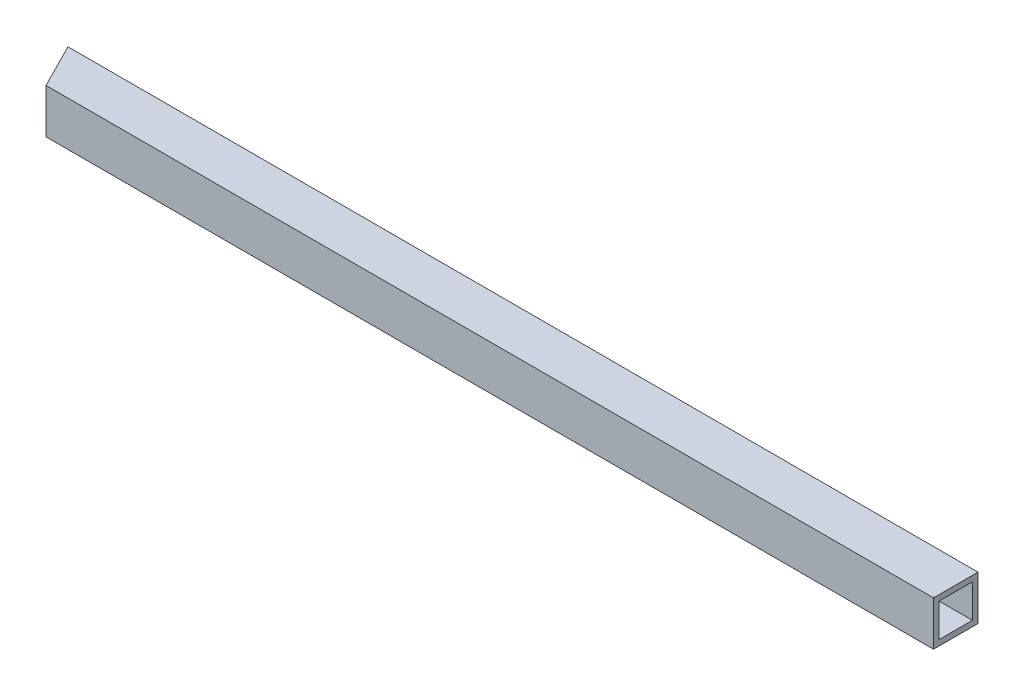
SolidWorks part; units mm, degrees
material "AISI 302"
ref_plane "Front Plane" through (0, 0, 0) normal (0, 0, 1) x (1, 0, 0)
ref_plane "Top Plane" through (0, 0, 0) normal (0, 1, 0) x (1, 0, 0)
ref_plane "Right Plane" through (0, 0, 0) normal (1, 0, 0) x (0, 0, -1)
sketch "Sketch2" plane through (0, 0, 0) normal (0, 0, 1) x (1, 0, 0)
  line L1 (0, 0) -> (4155.694, 0)
  line L2 (0, 0) -> (0, 203.2)
  line L3 (0, 203.2) -> (4155.694, 203.2)
  line L4 (4155.694, 0) -> (4155.694, 203.2)
  dimension "D1" = 203.2
  dimension "D2" = 4155.694
extrude "Boss-Extrude1" add sketch "Sketch2" along normal blind 203.2
sketch "Sketch3" plane through (0, 0, 0) normal (-1, 0, 0) x (0, 0, 1)
  line L8 (25.4, 25.4) -> (177.8, 25.4)
  line L9 (177.8, 25.4) -> (177.8, 177.8)
  line L10 (177.8, 177.8) -> (25.4, 177.8)
  line L11 (25.4, 177.8) -> (25.4, 25.4)
  line L12 (25.4, 25.4) -> (177.8, 25.4)
  line L13 (177.8, 25.4) -> (177.8, 177.8)
  line L14 (177.8, 177.8) -> (25.4, 177.8)
  line L15 (25.4, 177.8) -> (25.4, 25.4)
  dimension "D1" = 25.4
extrude "Cut-Extrude1" cut sketch "Sketch3" against normal through all both and the other way through all
sketch "Sketch4" plane through (0, 203.2, 0) normal (0, 1, 0) x (1, 0, 0)
  line L0 (0, 0) -> (102.8664, -203.2)
  line L1 (4155.694, -203.2) -> (0, -203.2) construction
  line L2 (0, -203.2) -> (0, 0) construction
  line L3 (102.8664, -203.2) -> (0, -203.2)
  line L4 (0, -203.2) -> (0, 0)
  dimension "D1" = 26.85
extrude "Cut-Extrude2" cut sketch "Sketch4" against normal through all both and the other way through all
